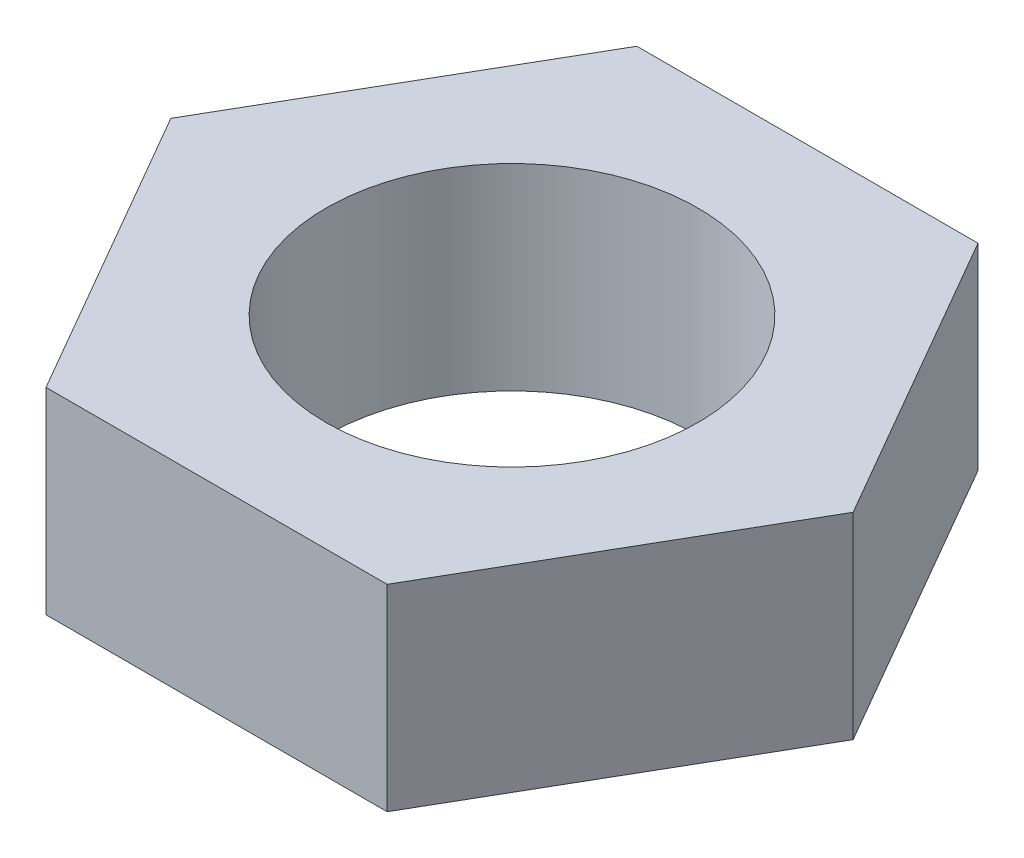
SolidWorks part; units mm, degrees
ref_plane "Front Plane" through (0, 0, 0) normal (0, 0, 1) x (1, 0, 0)
ref_plane "Top Plane" through (0, 0, 0) normal (0, 1, 0) x (1, 0, 0)
ref_plane "Right Plane" through (0, 0, 0) normal (1, 0, 0) x (0, 0, -1)
sketch "Sketch1" plane through (0, 0, 0) normal (0, 1, 0) x (1, 0, 0)
  line L1 (1.3748, 2.3812) -> (-1.3748, 2.3812)
  line L2 (-1.3748, 2.3812) -> (-2.7496, 0)
  line L3 (-2.7496, 0) -> (-1.3748, -2.3813)
  line L4 (-1.3748, -2.3813) -> (1.3748, -2.3813)
  line L5 (1.3748, -2.3813) -> (2.7496, 0)
  line L6 (2.7496, 0) -> (1.3748, 2.3812)
  circle A0 centre (0, 0) radius 2.3813 construction
  circle A1 centre (0, 0) radius 1.4986
  dimension "D2" = 2.9972
  dimension "D1" = 4.7625
extrude "Boss-Extrude1" add sketch "Sketch1" along normal blind 1.5875
